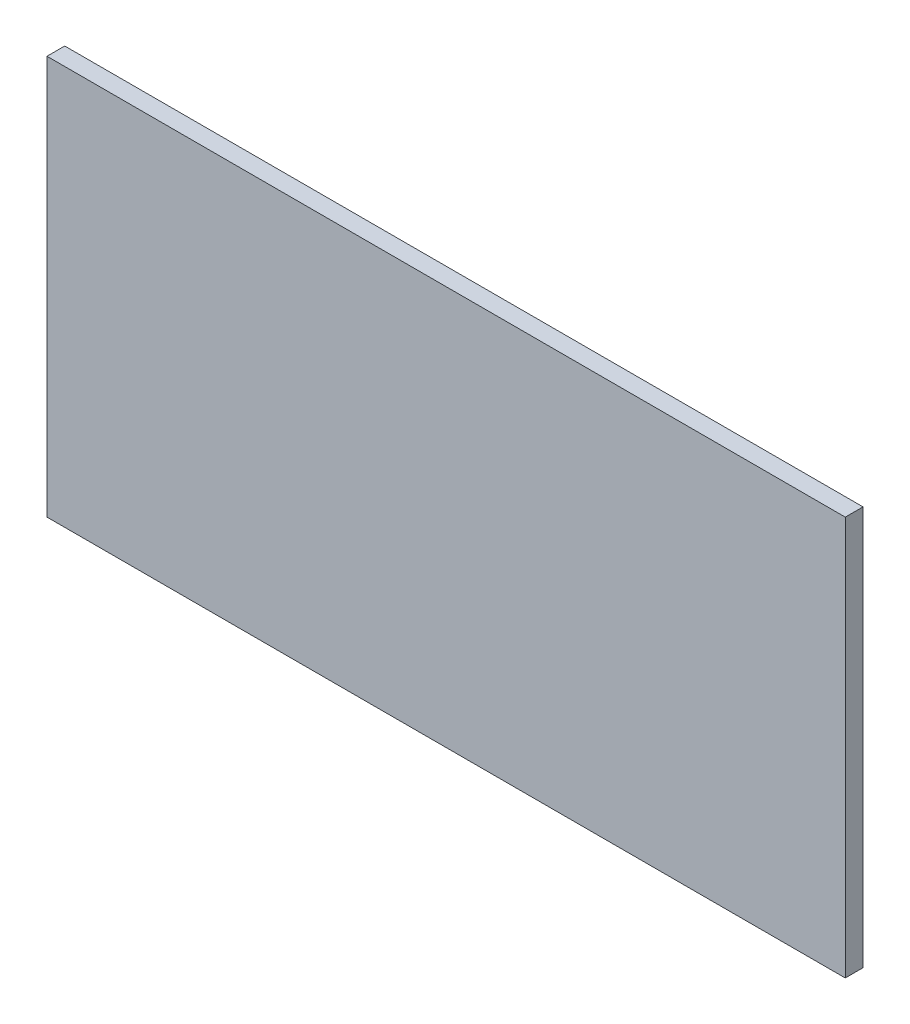
SolidWorks part; units mm, degrees
ref_plane "Alzado" through (0, 0, 0) normal (0, 0, 1) x (1, 0, 0)
ref_plane "Planta" through (0, 0, 0) normal (0, 1, 0) x (1, 0, 0)
ref_plane "Vista lateral" through (0, 0, 0) normal (1, 0, 0) x (0, 0, -1)
sketch "Croquis1" plane through (0, 0, 0) normal (0, 0, 1) x (1, 0, 0)
  line L1 (-560.2596, 291.9685) -> (339.7404, 291.9685)
  line L2 (-560.2596, 291.9685) -> (-560.2596, -158.0315)
  line L3 (-560.2596, -158.0315) -> (339.7404, -158.0315)
  line L4 (339.7404, 291.9685) -> (339.7404, -158.0315)
  dimension "D1" = 900
  dimension "D2" = 450
extrude "Saliente-Extruir1" add sketch "Croquis1" along normal blind 20
